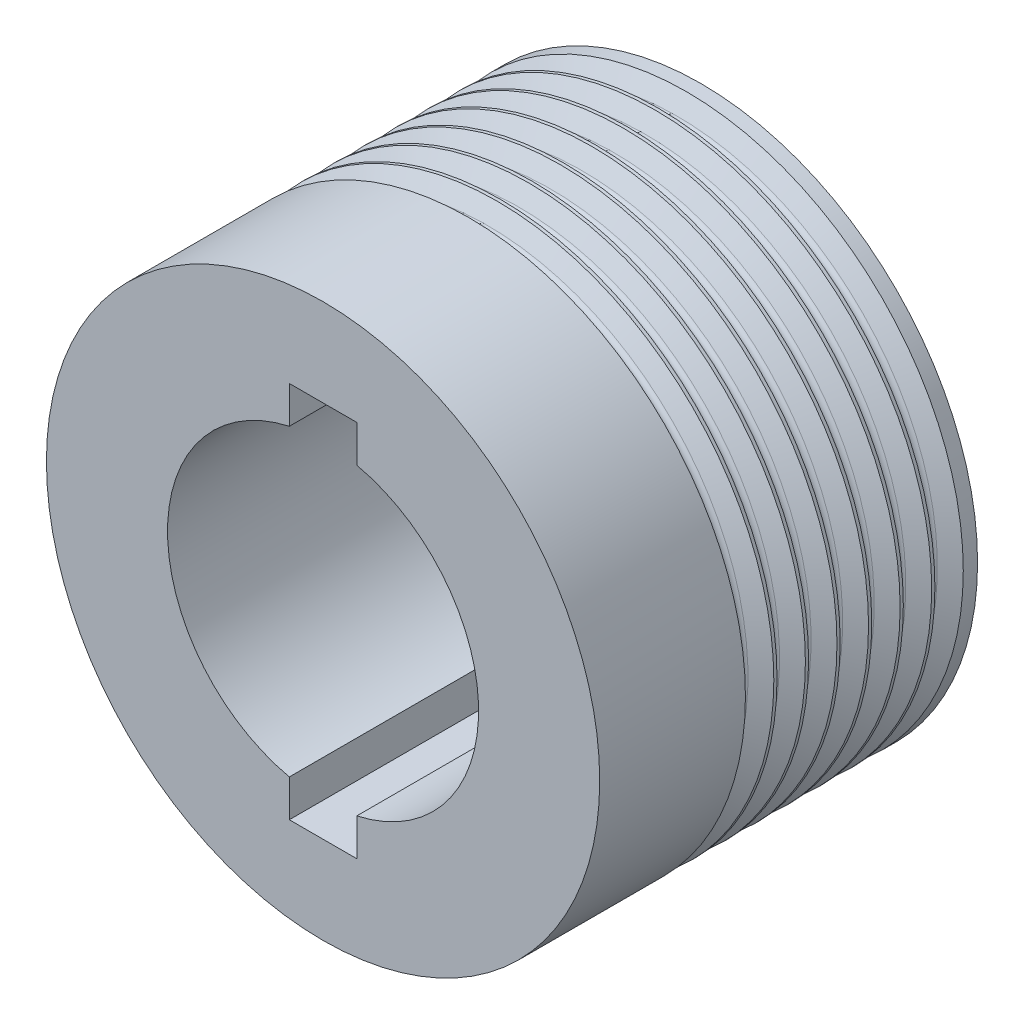
SolidWorks part; units mm, degrees
ref_plane "前视基准面" through (0, 0, 0) normal (0, 0, 1) x (1, 0, 0)
ref_plane "上视基准面" through (0, 0, 0) normal (0, 1, 0) x (1, 0, 0)
ref_plane "右视基准面" through (0, 0, 0) normal (1, 0, 0) x (0, 0, -1)
other "Configuration Table"
sketch "草图1" plane through (0, 0, 0) normal (0, 0, 1) x (1, 0, 0)
  circle A0 centre (0, 0) radius 20.5
  circle A1 centre (0, 0) radius 11.525
  dimension "D1" = 41
  dimension "D2" = 23.05
extrude "凸台-拉伸1" add sketch "草图1" along normal blind 28
sketch "草图2" plane through (0, 0, 0) normal (1, 0, 0) x (0, 0, -1)
  line L0 (-1, 24.3292) -> (-1, 7.0394) construction
  line L1 (0, -20.5) -> (0, 20.5) construction
  line L2 (-0.6062, 20.7) -> (-12.596, 20.7) construction
  line L3 (0, 20.5) -> (-28, 20.5) construction
  line L4 (-3.22, 20.6) -> (-1, 20.6)
  line L5 (-1, 20.6) -> (-1.7662, 19.29)
  line L6 (-2.4571, 19.2906) -> (-3.22, 20.6)
  line L7 (-3.34, 20.6) -> (-4.1062, 19.29)
  line L8 (-4.7971, 19.2906) -> (-5.56, 20.6)
  line L9 (-5.56, 20.6) -> (-3.34, 20.6)
  line L10 (-5.68, 20.6) -> (-6.4462, 19.29)
  line L11 (-7.1371, 19.2906) -> (-7.9, 20.6)
  line L12 (-7.9, 20.6) -> (-5.68, 20.6)
  line L13 (-8.02, 20.6) -> (-8.7862, 19.29)
  line L14 (-9.4771, 19.2906) -> (-10.24, 20.6)
  line L15 (-10.24, 20.6) -> (-8.02, 20.6)
  line L16 (-10.36, 20.6) -> (-11.1262, 19.29)
  line L17 (-11.8171, 19.2906) -> (-12.58, 20.6)
  line L18 (-12.58, 20.6) -> (-10.36, 20.6)
  line L19 (-12.7, 20.6) -> (-13.4662, 19.29)
  line L20 (-14.1571, 19.2906) -> (-14.92, 20.6)
  line L21 (-14.92, 20.6) -> (-12.7, 20.6)
  line L22 (-15.04, 20.6) -> (-15.8062, 19.29)
  line L23 (-16.4971, 19.2906) -> (-17.26, 20.6)
  line L24 (-17.26, 20.6) -> (-15.04, 20.6)
  line L28 (0, 0) -> (-30.5604, 0) construction
  line L29 (-17.38, 20.6) -> (-18.1462, 19.29) [skipped]
  line L30 (-18.8371, 19.2906) -> (-19.6, 20.6) [skipped]
  line L31 (-19.6, 20.6) -> (-17.38, 20.6) [skipped]
  arc A0 (-2.4571, 19.2906) -> (-1.7662, 19.29) centre (-2.1115, 19.492) ccw
  arc A1 (-4.7971, 19.2906) -> (-4.1062, 19.29) centre (-4.4515, 19.492) ccw
  arc A2 (-7.1371, 19.2906) -> (-6.4462, 19.29) centre (-6.7915, 19.492) ccw
  arc A3 (-9.4771, 19.2906) -> (-8.7862, 19.29) centre (-9.1315, 19.492) ccw
  arc A4 (-11.8171, 19.2906) -> (-11.1262, 19.29) centre (-11.4715, 19.492) ccw
  arc A5 (-14.1571, 19.2906) -> (-13.4662, 19.29) centre (-13.8115, 19.492) ccw
  arc A6 (-16.4971, 19.2906) -> (-15.8062, 19.29) centre (-16.1515, 19.492) ccw
  arc A8 (-18.8371, 19.2906) -> (-18.1462, 19.29) centre (-18.4915, 19.492) ccw [skipped]
  point P45 (0, 0)
  dimension "D6" = 0.4
  dimension "D1" = 1
  dimension "D2" = 0.2
  dimension "D3" = 0.1
  dimension "D4" = 8
  dimension "D5" = 1.31
  dimension "D7" = 2.22
revolve "切除-旋转1" cut sketch "草图2" angle 360 about L28
sketch "草图3" plane through (0, 0, 0) normal (0, 0, -1) x (-1, 0, 0)
  line L0 (0, 0) -> (0, -25.3755) construction
  line L1 (-2.5, 14) -> (2.5, 14)
  line L2 (-2.5, 14) -> (-2.5, -14)
  line L3 (-2.5, -14) -> (2.5, -14)
  line L4 (2.5, 14) -> (2.5, -14)
  dimension "D1" = 5
  dimension "D2" = 2.5
  dimension "D3" = 28
  dimension "D4" = 14
extrude "切除-拉伸1" cut sketch "草图3" against normal through all
